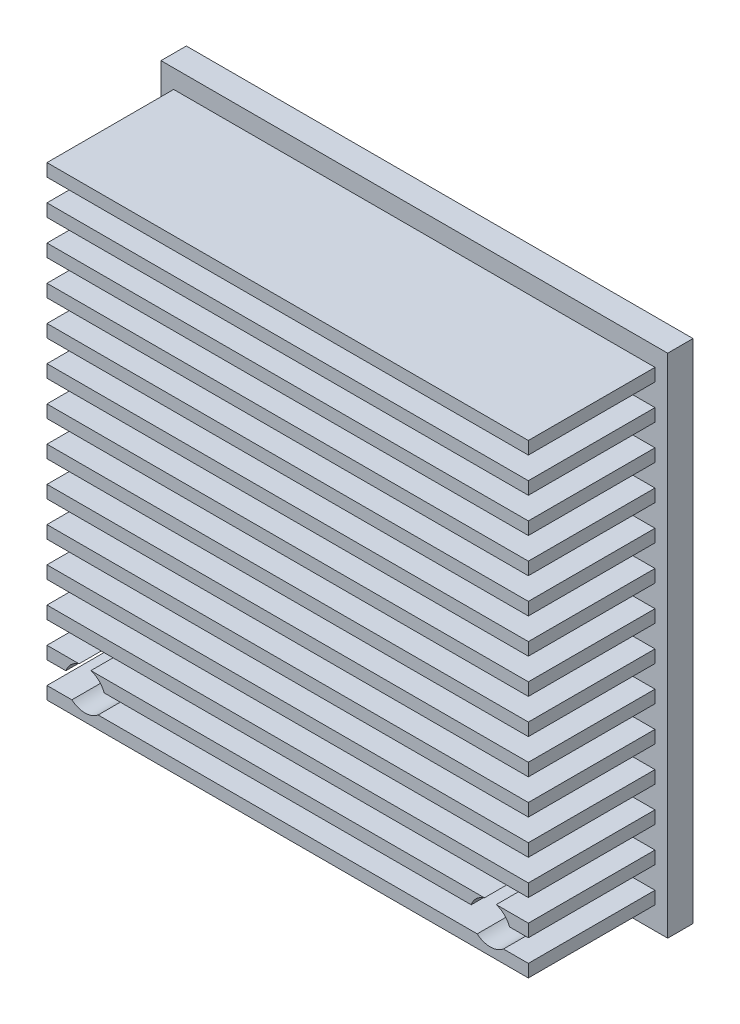
SolidWorks part; units mm, degrees
material "6061-T6 Black anodised"
ref_plane "Front Plane" through (0, 0, 0) normal (0, 0, 1) x (1, 0, 0)
ref_plane "Top Plane" through (0, 0, 0) normal (0, 1, 0) x (1, 0, 0)
ref_plane "Right Plane" through (0, 0, 0) normal (1, 0, 0) x (0, 0, -1)
sketch "Sketch1" plane through (0, 0, 0) normal (0, 0, 1) x (1, 0, 0)
  line L1 (20, 20) -> (-20, 20)
  line L2 (20, 20) -> (20, -20)
  line L3 (20, -20) -> (-20, -20)
  line L4 (-20, 20) -> (-20, -20)
  line L5 (20, 20) -> (-20, -20) construction
  line L6 (20, -20) -> (-20, 20) construction
  point P0 (0, 0)
  dimension "D1" = 40
extrude "Boss-Extrude1" add sketch "Sketch1" along normal blind 2
sketch "Sketch2" plane through (0, 0, 2) normal (0, 0, 1) x (1, 0, 0)
  line L0 (-19, 15.7807) -> (19, 15.7807)
  line L1 (-19, 18.5307) -> (19, 18.5307)
  line L2 (-19, 18.5307) -> (-19, 17.5307)
  line L3 (-19, 17.5307) -> (19, 17.5307)
  line L4 (19, 18.5307) -> (19, 17.5307)
  line L5 (-19, 18.5307) -> (19, 17.5307) construction
  line L6 (-19, 17.5307) -> (19, 18.5307) construction
  line L7 (-19, 15.7807) -> (-19, 14.7807)
  line L8 (-19, 14.7807) -> (19, 14.7807)
  line L9 (19, 15.7807) -> (19, 14.7807)
  line L10 (-19, 15.7807) -> (19, 14.7807) construction
  line L11 (-19, 14.7807) -> (19, 15.7807) construction
  line L12 (-19, 13.0307) -> (19, 13.0307)
  line L13 (-19, 13.0307) -> (-19, 12.0307)
  line L14 (-19, 12.0307) -> (19, 12.0307)
  line L15 (19, 13.0307) -> (19, 12.0307)
  line L16 (-19, 13.0307) -> (19, 12.0307) construction
  line L17 (-19, 12.0307) -> (19, 13.0307) construction
  line L18 (-19, 10.2807) -> (19, 10.2807)
  line L19 (-19, 10.2807) -> (-19, 9.2807)
  line L20 (-19, 9.2807) -> (19, 9.2807)
  line L21 (19, 10.2807) -> (19, 9.2807)
  line L22 (-19, 10.2807) -> (19, 9.2807) construction
  line L23 (-19, 9.2807) -> (19, 10.2807) construction
  line L24 (-19, 7.5307) -> (19, 7.5307)
  line L25 (-19, 7.5307) -> (-19, 6.5307)
  line L26 (-19, 6.5307) -> (19, 6.5307)
  line L27 (19, 7.5307) -> (19, 6.5307)
  line L28 (-19, 7.5307) -> (19, 6.5307) construction
  line L29 (-19, 6.5307) -> (19, 7.5307) construction
  line L30 (-19, 4.7807) -> (19, 4.7807)
  line L31 (-19, 4.7807) -> (-19, 3.7807)
  line L32 (-19, 3.7807) -> (19, 3.7807)
  line L33 (19, 4.7807) -> (19, 3.7807)
  line L34 (-19, 4.7807) -> (19, 3.7807) construction
  line L35 (-19, 3.7807) -> (19, 4.7807) construction
  line L36 (-19, 2.0307) -> (19, 2.0307)
  line L37 (-19, 2.0307) -> (-19, 1.0307)
  line L38 (-19, 1.0307) -> (19, 1.0307)
  line L39 (19, 2.0307) -> (19, 1.0307)
  line L40 (-19, 2.0307) -> (19, 1.0307) construction
  line L41 (-19, 1.0307) -> (19, 2.0307) construction
  line L42 (-19, -0.7193) -> (19, -0.7193)
  line L43 (-19, -0.7193) -> (-19, -1.7193)
  line L44 (-19, -1.7193) -> (19, -1.7193)
  line L45 (19, -0.7193) -> (19, -1.7193)
  line L46 (-19, -0.7193) -> (19, -1.7193) construction
  line L47 (-19, -1.7193) -> (19, -0.7193) construction
  line L48 (-19, -3.4693) -> (19, -3.4693)
  line L49 (-19, -3.4693) -> (-19, -4.4693)
  line L50 (-19, -4.4693) -> (19, -4.4693)
  line L51 (19, -3.4693) -> (19, -4.4693)
  line L52 (-19, -3.4693) -> (19, -4.4693) construction
  line L53 (-19, -4.4693) -> (19, -3.4693) construction
  line L54 (-19, -6.2193) -> (19, -6.2193)
  line L55 (-19, -6.2193) -> (-19, -7.2193)
  line L56 (-19, -7.2193) -> (19, -7.2193)
  line L57 (19, -6.2193) -> (19, -7.2193)
  line L58 (-19, -6.2193) -> (19, -7.2193) construction
  line L59 (-19, -7.2193) -> (19, -6.2193) construction
  line L60 (-19, -8.9693) -> (19, -8.9693)
  line L61 (-19, -8.9693) -> (-19, -9.9693)
  line L62 (-19, -9.9693) -> (19, -9.9693)
  line L63 (19, -8.9693) -> (19, -9.9693)
  line L64 (-19, -8.9693) -> (19, -9.9693) construction
  line L65 (-19, -9.9693) -> (19, -8.9693) construction
  line L66 (-19, -11.7193) -> (19, -11.7193)
  line L67 (-19, -11.7193) -> (-19, -12.7193)
  line L68 (-19, -12.7193) -> (19, -12.7193)
  line L69 (19, -11.7193) -> (19, -12.7193)
  line L70 (-19, -11.7193) -> (19, -12.7193) construction
  line L71 (-19, -12.7193) -> (19, -11.7193) construction
  line L72 (-19, -14.4693) -> (19, -14.4693)
  line L73 (-19, -14.4693) -> (-19, -15.4693)
  line L74 (-19, -15.4693) -> (19, -15.4693)
  line L75 (19, -14.4693) -> (19, -15.4693)
  line L76 (-19, -14.4693) -> (19, -15.4693) construction
  line L77 (-19, -15.4693) -> (19, -14.4693) construction
  line L78 (-19, -17.2193) -> (19, -17.2193)
  line L79 (-19, -17.2193) -> (-19, -18.2193)
  line L80 (-19, -18.2193) -> (19, -18.2193)
  line L81 (19, -17.2193) -> (19, -18.2193)
  line L82 (-19, -17.2193) -> (19, -18.2193) construction
  line L83 (-19, -18.2193) -> (19, -17.2193) construction
  point P0 (0, 18.0307)
  point P8 (0, 15.2807)
  point P13 (0, 12.5307)
  point P18 (0, 9.7807)
  point P23 (0, 7.0307)
  point P28 (0, 4.2807)
  point P33 (0, 1.5307)
  point P38 (0, -1.2193)
  point P43 (0, -3.9693)
  point P48 (0, -6.7193)
  point P53 (0, -9.4693)
  point P58 (0, -12.2193)
  point P63 (0, -14.9693)
  point P68 (0, -17.7193)
  dimension "D1" = 1
  dimension "D2" = 38
  dimension "D3" = 14
extrude "Boss-Extrude2" add sketch "Sketch2" along normal blind 10
sketch "Sketch3" plane through (0, 0, 0) normal (0, 0, -1) x (-1, 0, 0)
  line L0 (-16, -16) -> (16, -16) construction
  line L1 (-12.75, -14) -> (12.75, -14) construction
  line L2 (20, -20) -> (-20, -20) construction
  circle A0 centre (16, -16) radius 1.6
  circle A1 centre (-16, -16) radius 1.6
  circle A2 centre (12.75, -14) radius 1.6 construction
  circle A3 centre (-12.75, -14) radius 1.6 construction
  circle A4 centre (0, -14) radius 1.6 construction
  point P2 (0, -16)
  point P8 (0, -14)
  dimension "D1" = 3.2
  dimension "D4" = 3.2
  dimension "D2" = 32
  dimension "D3" = 16
  dimension "D5" = 25.5
  dimension "D6" = 6
extrude "Cut-Extrude1" cut sketch "Sketch3" against normal through all
